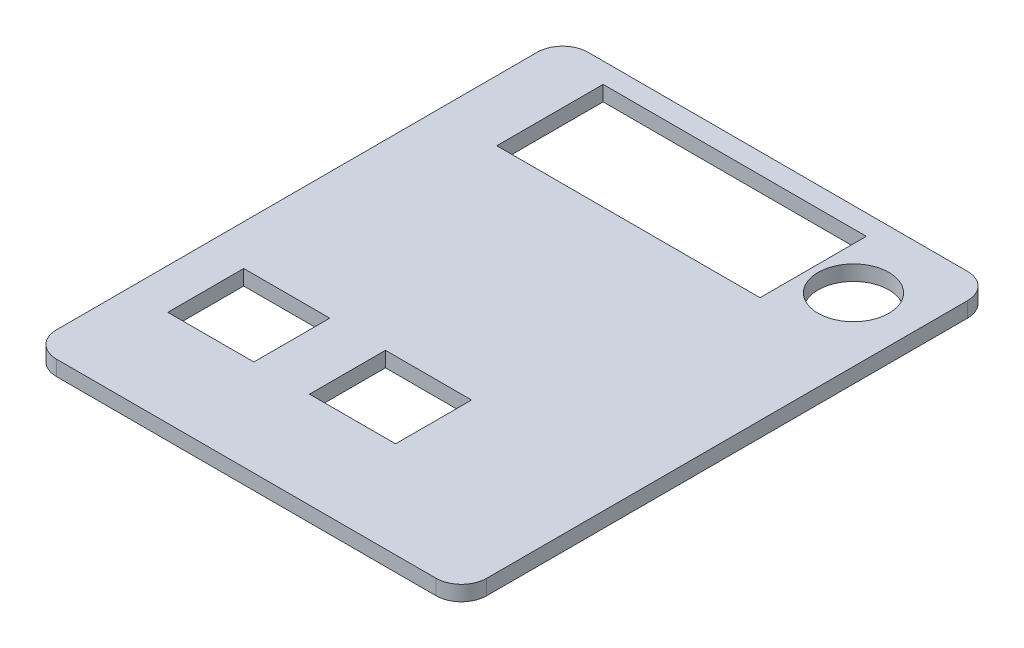
SolidWorks part; units mm, degrees
ref_plane "Front Plane" through (0, 0, 0) normal (0, 0, 1) x (1, 0, 0)
ref_plane "Top Plane" through (0, 0, 0) normal (0, 1, 0) x (1, 0, 0)
ref_plane "Right Plane" through (0, 0, 0) normal (1, 0, 0) x (0, 0, -1)
sketch "Sketch1" plane through (0, 0, 0) normal (0, 1, 0) x (1, 0, 0)
  line L1 (-42.5, -52.5) -> (42.5, -52.5)
  line L2 (-42.5, -52.5) -> (-42.5, 52.5)
  line L3 (-42.5, 52.5) -> (42.5, 52.5)
  line L4 (42.5, -52.5) -> (42.5, 52.5)
  line L5 (-42.5, -52.5) -> (42.5, 52.5) construction
  line L6 (-42.5, 52.5) -> (42.5, -52.5) construction
  point P0 (0, 0)
  dimension "D1" = 85
  dimension "D2" = 105
extrude "Boss-Extrude1" add sketch "Sketch1" along normal blind 3
sketch "Sketch2" plane through (0, 3, 0) normal (0, 1, 0) x (1, 0, 0)
  line L0 (-42.5, -52.5) -> (42.5, -52.5) construction
  line L1 (-34.5, -33.5) -> (-17.5, -33.5)
  line L2 (-34.5, -33.5) -> (-34.5, -18.5)
  line L3 (-34.5, -18.5) -> (-17.5, -18.5)
  line L4 (-17.5, -33.5) -> (-17.5, -18.5)
  line L5 (-34.5, -33.5) -> (-17.5, -18.5) construction
  line L6 (-34.5, -18.5) -> (-17.5, -33.5) construction
  line L7 (-6.5, -33.5) -> (10.5, -33.5)
  line L8 (-6.5, -33.5) -> (-6.5, -18.5)
  line L9 (-6.5, -18.5) -> (10.5, -18.5)
  line L10 (10.5, -33.5) -> (10.5, -18.5)
  line L11 (-6.5, -33.5) -> (10.5, -18.5) construction
  line L12 (-6.5, -18.5) -> (10.5, -33.5) construction
  line L13 (-42.5, 52.5) -> (-42.5, -52.5) construction
  point P0 (-26, -26)
  point P5 (2, -26)
  dimension "D1" = 19
  dimension "D2" = 19
  dimension "D3" = 34
  dimension "D4" = 34
  dimension "D5" = 8
  dimension "D6" = 25
  dimension "D7" = 36
  dimension "D8" = 53
extrude "Cut-Extrude1" cut sketch "Sketch2" against normal blind 10
fillet "Fillet1" radius 5 4 edges at (-42.5, 1.5, -52.5) (42.5, 1.5, -52.5) (42.5, 1.5, 52.5) (-42.5, 1.5, 52.5)
sketch "Sketch3" plane through (0, 3, 0) normal (0, 1, 0) x (1, 0, 0)
  line L0 (37.5, 52.5) -> (-37.5, 52.5) construction
  line L1 (-30.5, 48.5) -> (21.5, 48.5)
  line L2 (-30.5, 48.5) -> (-30.5, 27.5)
  line L3 (-30.5, 27.5) -> (21.5, 27.5)
  line L4 (21.5, 48.5) -> (21.5, 27.5)
  line L5 (-42.5, 47.5) -> (-42.5, -47.5) construction
  dimension "D1" = 4
  dimension "D2" = 25
  dimension "D3" = 12
  dimension "D4" = 64
extrude "Cut-Extrude2" cut sketch "Sketch3" against normal blind 10
sketch "Sketch4" plane through (0, 3, 0) normal (0, 1, 0) x (1, 0, 0)
  circle A0 centre (29.8979, 37.5654) radius 7
  dimension "D1" = 14
extrude "Cut-Extrude3" cut sketch "Sketch4" against normal blind 10
